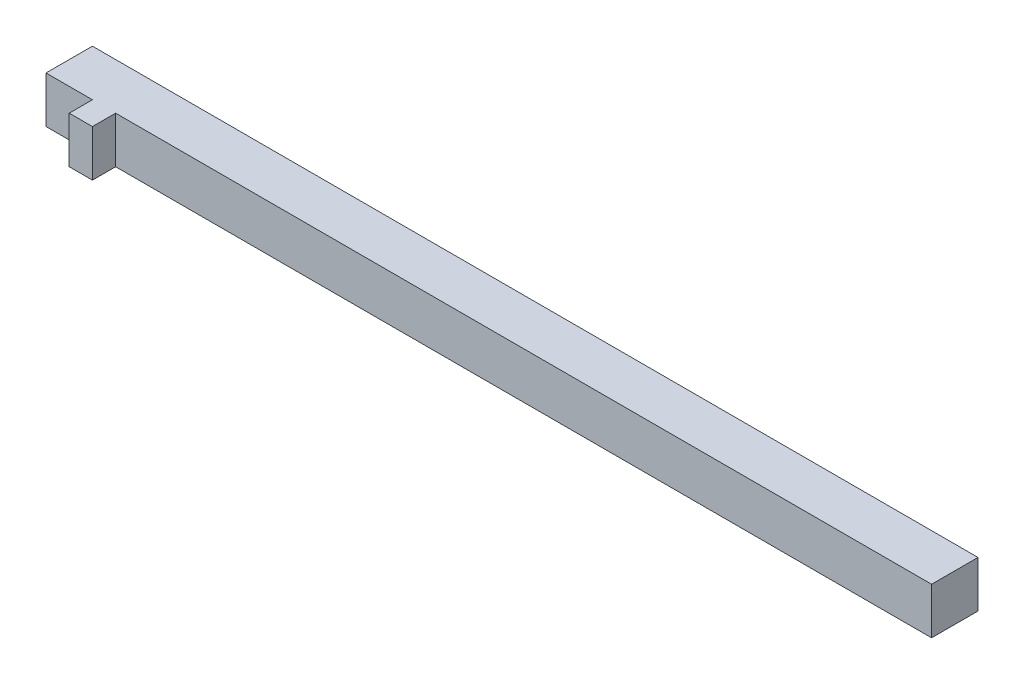
SolidWorks part; units mm, degrees
ref_plane "Alzado" through (0, 0, 0) normal (0, 0, 1) x (1, 0, 0)
ref_plane "Planta" through (0, 0, 0) normal (0, 1, 0) x (1, 0, 0)
ref_plane "Vista lateral" through (0, 0, 0) normal (1, 0, 0) x (0, 0, -1)
sketch "Croquis1" plane through (0, 0, 0) normal (0, 0, 1) x (1, 0, 0)
  line L1 (1907.5, -100) -> (-1907.5, -100)
  line L2 (1907.5, -100) -> (1907.5, 100)
  line L3 (1907.5, 100) -> (-1907.5, 100)
  line L4 (-1907.5, -100) -> (-1907.5, 100)
  line L5 (1907.5, -100) -> (-1907.5, 100) construction
  line L6 (1907.5, 100) -> (-1907.5, -100) construction
  point P0 (0, 0)
  dimension "D1" = 3815
  dimension "D2" = 200
extrude "Saliente-Extruir1" add sketch "Croquis1" along normal blind 200
sketch "Croquis3" plane through (0, 0, 200) normal (0, 0, 1) x (1, 0, 0)
  line L5 (-1850, 0) -> (-1650, 0) construction
  line L6 (-1907.5, -100) -> (1907.5, -100) construction
  line L7 (-1707.5, -100) -> (-1607.5, -100)
  line L8 (-1707.5, -100) -> (-1707.5, 100)
  line L9 (-1707.5, 100) -> (-1607.5, 100)
  line L10 (-1607.5, -100) -> (-1607.5, 100)
  line L11 (1907.5, 100) -> (-1907.5, 100) construction
  line L12 (-1907.5, 100) -> (-1907.5, -100) construction
  dimension "D1" = 200
  dimension "D2" = 200
  dimension "D3" = 100
extrude "Saliente-Extruir6" add sketch "Croquis3" along normal blind 100
